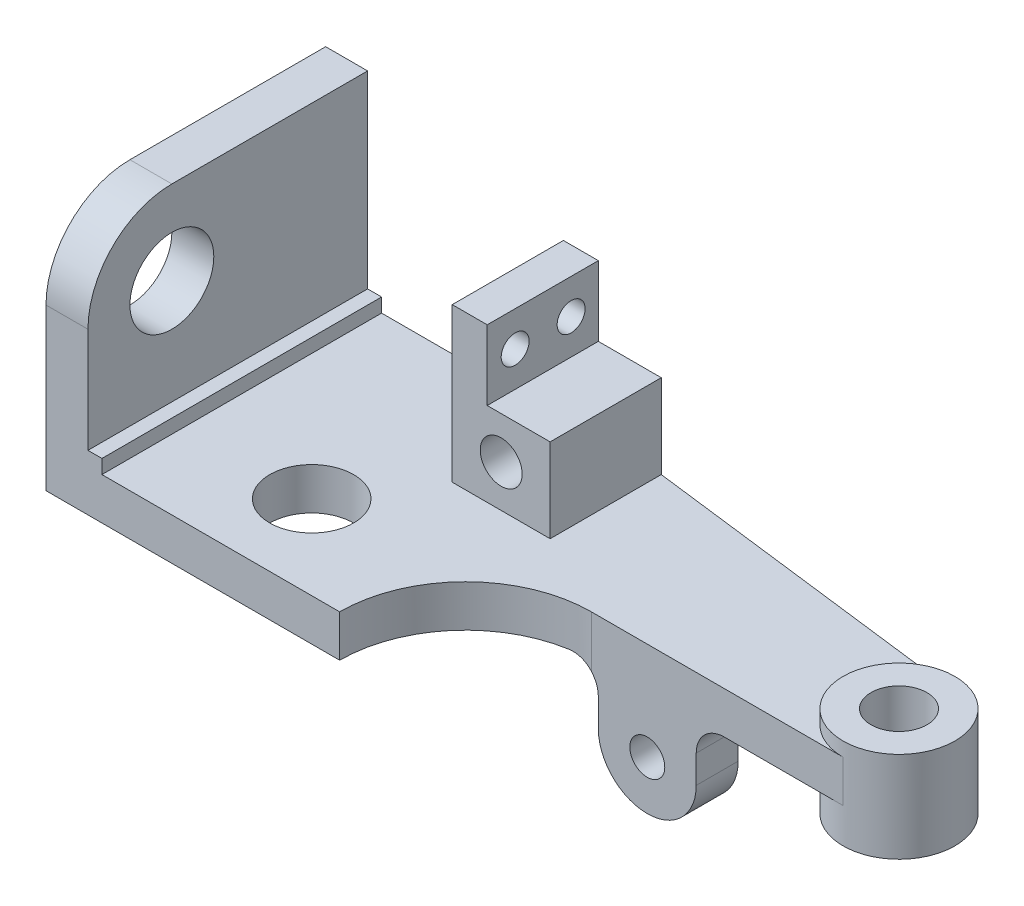
SolidWorks part; units mm, degrees
ref_plane "Alzado" through (0, 0, 0) normal (0, 0, 1) x (1, 0, 0)
ref_plane "Planta" through (0, 0, 0) normal (0, 1, 0) x (1, 0, 0)
ref_plane "Vista lateral" through (0, 0, 0) normal (1, 0, 0) x (0, 0, -1)
sketch "Croquis1" plane through (0, 0, 0) normal (0, 1, 0) x (1, 0, 0)
  line L0 (0, 0) -> (66.675, 0)
  line L1 (0, 0) -> (0, 63.5)
  line L2 (0, 63.5) -> (9.525, 63.5)
  line L3 (9.525, 63.5) -> (152.4, 63.5) construction
  line L4 (9.525, 63.5) -> (61.9125, 63.5)
  line L5 (61.9125, 63.5) -> (76.2, 63.5)
  line L6 (152.4, 63.5) -> (152.4, 41.275) construction
  line L7 (152.4, 53.975) -> (76.2, 63.5)
  line L8 (66.675, 0) -> (95.25, 0) construction
  line L9 (95.25, 0) -> (95.25, 28.575) construction
  line L10 (95.25, 28.575) -> (152.4, 28.575)
  line L13 (41.275, 0) -> (41.275, 19.05) construction
  arc A0 (152.4, 28.575) -> (152.4, 53.975) centre (152.4, 41.275) ccw
  arc A1 (66.675, 0) -> (95.25, 28.575) centre (95.25, 0) cw
  circle A2 centre (41.275, 19.05) radius 9.525
  dimension "D8" = 25.4
  dimension "D11" = 19.05
  dimension "D1" = 66.675
  dimension "D2" = 63.5
  dimension "D3" = 9.525
  dimension "D4" = 142.875
  dimension "D5" = 52.3875
  dimension "D6" = 14.2875
  dimension "D7" = 22.225
  dimension "D9" = 28.575
  dimension "D10" = 41.275
  dimension "D12" = 19.05
extrude "Saliente-Extruir1" add sketch "Croquis1" along normal blind 9.525
sketch "Croquis2" plane through (0, 9.525, 0) normal (0, 1, 0) x (1, 0, 0)
  line L0 (152.4, 41.275) -> (107.95, 41.275) construction
  line L1 (0, 0) -> (9.525, 0)
  line L2 (0, 0) -> (0, 63.5)
  line L3 (0, 63.5) -> (9.525, 63.5)
  line L4 (9.525, 0) -> (9.525, 63.5)
  line L5 (107.95, 41.275) -> (107.95, 28.575) construction
  line L6 (95.25, 28.575) -> (152.4, 28.575) construction
  dimension "D1" = 44.45
extrude "Saliente-Extruir3" add sketch "Croquis2" along normal blind 46.0375
sketch "Croquis3" plane through (9.525, 0, 0) normal (1, 0, 0) x (0, 0, -1)
  line L0 (0, 55.5625) -> (19.05, 55.5625) construction
  line L1 (0, 55.5625) -> (63.5, 55.5625) construction
  line L2 (19.05, 55.5625) -> (19.05, 36.5125) construction
  line L3 (0, 55.5625) -> (0, 9.525) construction
  arc A0 (0, 36.5125) -> (19.05, 55.5625) centre (19.05, 36.5125) cw
  circle A1 centre (19.05, 36.5125) radius 9.525
  line M3 (63.5, 55.5625) -> (0, 55.5625)
  line M4 (0, 55.5625) -> (0, 9.525)
  dimension "D3" = 19.05
  dimension "D4" = 19.05
  dimension "D1" = 19.05
  dimension "D2" = 19.05
extrude "Cortar-Extruir1" cut sketch "Croquis3" against normal blind 46.0375 contours A1 | A0 M4 M3
sketch "Croquis4" plane through (0, 9.525, 0) normal (0, 1, 0) x (1, 0, 0)
  circle A0 centre (152.4, 41.275) radius 12.7
extrude "Saliente-Extruir4" add sketch "Croquis4" along normal blind 3.175
sketch "Croquis5" plane through (0, 9.525, 0) normal (0, 1, 0) x (1, 0, 0)
  line L1 (76.2, 63.5) -> (53.975, 63.5)
  line L2 (76.2, 63.5) -> (76.2, 38.2663)
  line L3 (76.2, 38.2663) -> (53.975, 38.2663)
  line L4 (53.975, 63.5) -> (53.975, 38.2663)
  dimension "D1" = 22.225
extrude "Saliente-Extruir5" add sketch "Croquis5" along normal blind 19.05
sketch "Croquis6" plane through (0, 28.575, 0) normal (0, 1, 0) x (1, 0, 0)
  line L0 (53.975, 38.2663) -> (76.2, 38.2663) construction
  line L1 (53.975, 63.5) -> (61.9125, 63.5)
  line L2 (53.975, 63.5) -> (53.975, 38.2663)
  line L3 (53.975, 38.2663) -> (61.9125, 38.2663)
  line L4 (61.9125, 63.5) -> (61.9125, 38.2663)
  dimension "D1" = 7.9375
extrude "Saliente-Extruir6" add sketch "Croquis6" along normal blind 15.875
sketch "Croquis7" plane through (61.9125, 0, 0) normal (1, 0, 0) x (0, 0, -1)
  line L0 (38.2663, 28.575) -> (38.2663, 36.5125) construction
  line L1 (38.2663, 44.45) -> (38.2663, 28.575) construction
  line L2 (38.2663, 36.5125) -> (44.6163, 36.5125) construction
  line L3 (44.6163, 36.5125) -> (57.3163, 36.5125) construction
  circle A0 centre (44.6163, 36.5125) radius 3.175
  circle A1 centre (57.3163, 36.5125) radius 3.175
  dimension "D4" = 6.35
  dimension "D1" = 7.9375
  dimension "D2" = 6.35
  dimension "D3" = 12.7
extrude "Cortar-Extruir2" cut sketch "Croquis7" against normal blind 15.875
sketch "Croquis8" plane through (0, 0, -38.2663) normal (0, 0, 1) x (1, 0, 0)
  line L0 (65.0875, 9.525) -> (65.0875, 19.05) construction
  line L1 (53.975, 9.525) -> (76.2, 9.525) construction
  circle A0 centre (65.0875, 19.05) radius 4.7625
  dimension "D2" = 9.525
  dimension "D1" = 9.525
extrude "Cortar-Extruir4" cut sketch "Croquis8" against normal through all
sketch "Croquis9" plane through (0, 0, 0) normal (0, -1, 0) x (1, 0, 0)
  circle A0 centre (152.4, -41.275) radius 12.7
extrude "Saliente-Extruir7" add sketch "Croquis9" along normal blind 7.9375
sketch "Croquis10" plane through (0, 12.7, 0) normal (0, 1, 0) x (1, 0, 0)
  circle A0 centre (152.4, 41.275) radius 6.35
  dimension "D1" = 12.7
extrude "Cortar-Extruir5" cut sketch "Croquis10" against normal through all
sketch "Croquis14" plane through (0, 0, 0) normal (0, -1, 0) x (1, 0, 0)
  line L0 (107.95, -41.275) -> (107.95, -28.575) construction
  line L1 (107.95, -41.275) -> (107.95, -28.575) construction
  line L2 (96.8375, -28.575) -> (119.0625, -28.575)
  line L3 (96.8375, -28.575) -> (96.8375, -38.1)
  line L4 (119.0625, -28.575) -> (119.0625, -38.1)
  line L5 (96.8375, -38.1) -> (119.0625, -38.1)
  point P4 (107.95, -28.575)
  dimension "D1" = 22.225
  dimension "D2" = 9.525
  dimension "D3" = 9.525
extrude "Saliente-Extruir8" add sketch "Croquis14" along normal blind 23.8125
sketch "Croquis15" plane through (0, 0, -28.575) normal (0, 0, 1) x (1, 0, 0)
  line L0 (107.95, -23.8125) -> (107.95, -12.7) construction
  line L1 (119.0625, -23.8125) -> (96.8375, -23.8125) construction
  line L2 (96.8375, -12.7) -> (119.0625, -12.7) construction
  arc A0 (96.8375, -12.7) -> (119.0625, -12.7) centre (107.95, -12.7) ccw
  circle A1 centre (107.95, -12.7) radius 3.9687
  point P6 (107.95, -12.7)
  line M2 (96.8375, 0) -> (96.8375, -23.8125)
  line M3 (96.8375, -23.8125) -> (119.0625, -23.8125)
  line M4 (119.0625, -23.8125) -> (119.0625, 0)
  dimension "D3" = 7.9375
  dimension "D1" = 11.1125
  dimension "D2" = 22.225
extrude "Cortar-Extruir7" cut sketch "Croquis15" against normal through all contours A1 | A0 M3 M4 | A0 M2 M3
fillet "Redondeo6" radius 6.35 2 edges at (119.0625, 0, -33.3375) (96.8375, 0, -33.3375)
sketch "Croquis16" plane through (0, 0, 0) normal (0, 0, 1) x (1, 0, 0)
  line L1 (9.525, 9.525) -> (12.7, 9.525)
  line L2 (9.525, 9.525) -> (9.525, 12.7)
  line L3 (9.525, 12.7) -> (12.7, 12.7)
  line L4 (12.7, 9.525) -> (12.7, 12.7)
  dimension "D1" = 3.175
  dimension "D2" = 3.175
extrude "Saliente-Extruir9" add sketch "Croquis16" against normal blind 63.5
